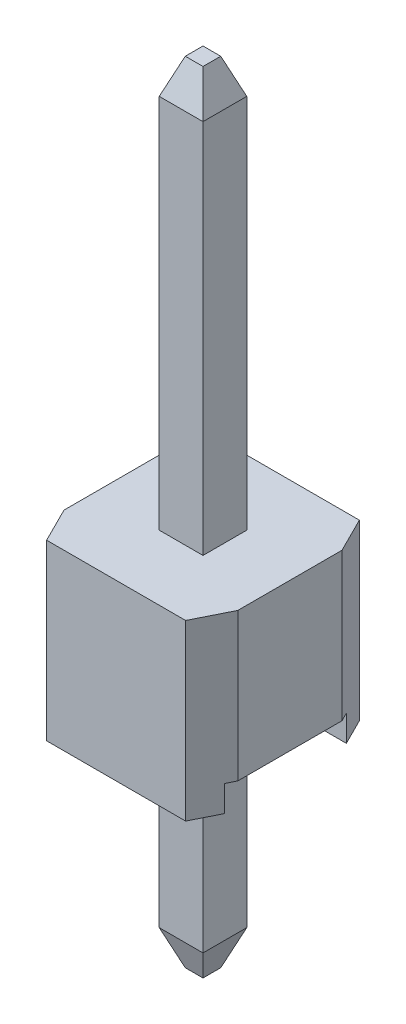
SolidWorks part; units mm, degrees
ref_plane "Front Plane" through (0, 0, 0) normal (0, 0, 1) x (1, 0, 0)
ref_plane "Top Plane" through (0, 0, 0) normal (0, 1, 0) x (1, 0, 0)
ref_plane "Right Plane" through (0, 0, 0) normal (1, 0, 0) x (0, 0, -1)
sketch "Sketch1" plane through (0, 0, 0) normal (0, 1, 0) x (1, 0, 0)
  line L1 (0, 0) -> (2.54, 0)
  line L2 (0, 0) -> (0, 2.54)
  line L3 (0, 2.54) -> (2.54, 2.54)
  line L4 (2.54, 0) -> (2.54, 2.54)
  dimension "D1" = 2.54
  dimension "D2" = 2.54
extrude "Main Body" add sketch "Sketch1" along normal blind 2.54
sketch "Sketch3" plane through (0, 0, 0) normal (-1, 0, 0) x (0, 0, 1)
  line L0 (-2.54, 0) -> (0, 0) construction
  line L1 (-2.159, 0) -> (-0.381, 0)
  line L2 (-2.159, 0) -> (-2.159, 0.381)
  line L3 (-2.159, 0.381) -> (-0.381, 0.381)
  line L4 (-0.381, 0) -> (-0.381, 0.381)
  line L5 (-2.54, 0) -> (-2.159, 0) construction
  line L6 (-0.381, 0) -> (0, 0) construction
  dimension "D1" = 0.381
extrude "Cut-Extrude1" cut sketch "Sketch3" against normal through all
sketch "Sketch4" plane through (0, 2.54, 0) normal (0, 1, 0) x (1, 0, 0)
  line L0 (0, 2.54) -> (0, 2.032)
  line L1 (0, 2.54) -> (0, 0) construction
  line L2 (0, 2.032) -> (0.254, 2.54)
  line L3 (2.54, 2.54) -> (0, 2.54) construction
  line L4 (0.254, 2.54) -> (0, 2.54)
  line L5 (2.54, 2.54) -> (2.286, 2.54)
  line L6 (2.286, 2.54) -> (2.54, 2.032)
  line L7 (2.54, 0) -> (2.54, 2.54) construction
  line L8 (2.54, 2.032) -> (2.54, 2.54)
  line L9 (2.54, 0) -> (2.286, 0)
  line L10 (0, 0) -> (2.54, 0) construction
  line L11 (2.286, 0) -> (2.54, 0.508)
  line L12 (2.54, 0.508) -> (2.54, 0)
  line L14 (0, 0) -> (0, 0.508)
  line L15 (0, 0.508) -> (0.254, 0)
  line L16 (0.254, 0) -> (0, 0)
  line M1 (0, 2.54) -> (0, 0)
  line M2 (0, 0) -> (2.54, 0)
  line M3 (2.54, 0) -> (2.54, 2.54)
  line M4 (2.54, 2.54) -> (0, 2.54)
  dimension "D1" = 0.254
  dimension "D2" = 0.508
extrude "Cut-Extrude2" cut sketch "Sketch4" against normal through all contours L2 M1 M4 | L6 M4 M3 | L15 M1 M2 | L9 L11 L12
sketch "Sketch2" plane through (0, 2.54, 0) normal (0, 1, 0) x (1, 0, 0)
  line L0 (1.27, 2.54) -> (1.27, 1.59) construction
  line L1 (0.95, 0.95) -> (1.59, 0.95)
  line L2 (0.95, 0.95) -> (0.95, 1.59)
  line L3 (0.95, 1.59) -> (1.59, 1.59)
  line L4 (1.59, 0.95) -> (1.59, 1.59)
  line L6 (2.286, 2.54) -> (0.254, 2.54) construction
  line L8 (1.27, 0.95) -> (1.27, 0) construction
  line L9 (0.254, 0) -> (2.286, 0) construction
  dimension "D1" = 0.64
extrude "Pin" add sketch "Sketch2" along normal blind 6 and the other way offset from surface (5.54 mm away) 3 other way up to face at (1.27, 0, -0.1905)
chamfer "Chamfer1" distance 0.508 distance2 0.1905 4 edges at (0.95, 8.54, -1.27) (1.27, 8.54, -1.59) (1.59, 8.54, -1.27) (1.27, 8.54, -0.95)
chamfer "Chamfer2" distance 0.1905 distance2 0.508 4 edges at (1.27, -3, -1.59) (1.59, -3, -1.27) (1.27, -3, -0.95) (0.95, -3, -1.27)
